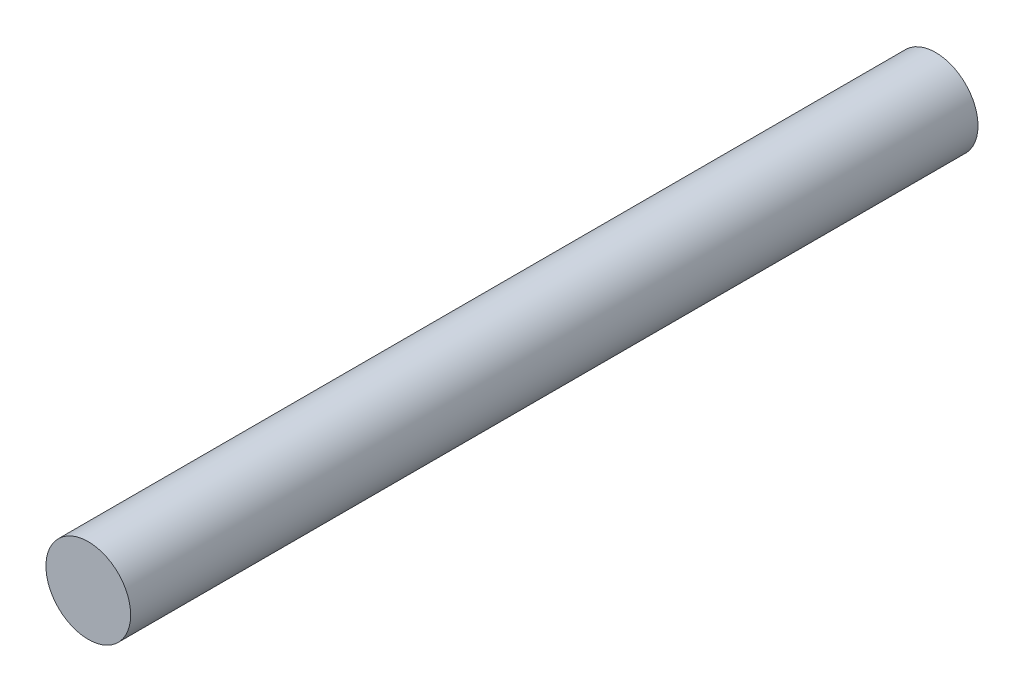
SolidWorks part; units mm, degrees
ref_plane "Alzado" through (0, 0, 0) normal (0, 0, 1) x (1, 0, 0)
ref_plane "Planta" through (0, 0, 0) normal (0, 1, 0) x (1, 0, 0)
ref_plane "Vista lateral" through (0, 0, 0) normal (1, 0, 0) x (0, 0, -1)
sketch "Croquis1" plane through (0, 0, 0) normal (0, 0, 1) x (1, 0, 0)
  circle A0 centre (0, 0) radius 0.1
  dimension "D1" = 0.2
extrude "Saliente-Extruir1" add sketch "Croquis1" along normal blind 2
